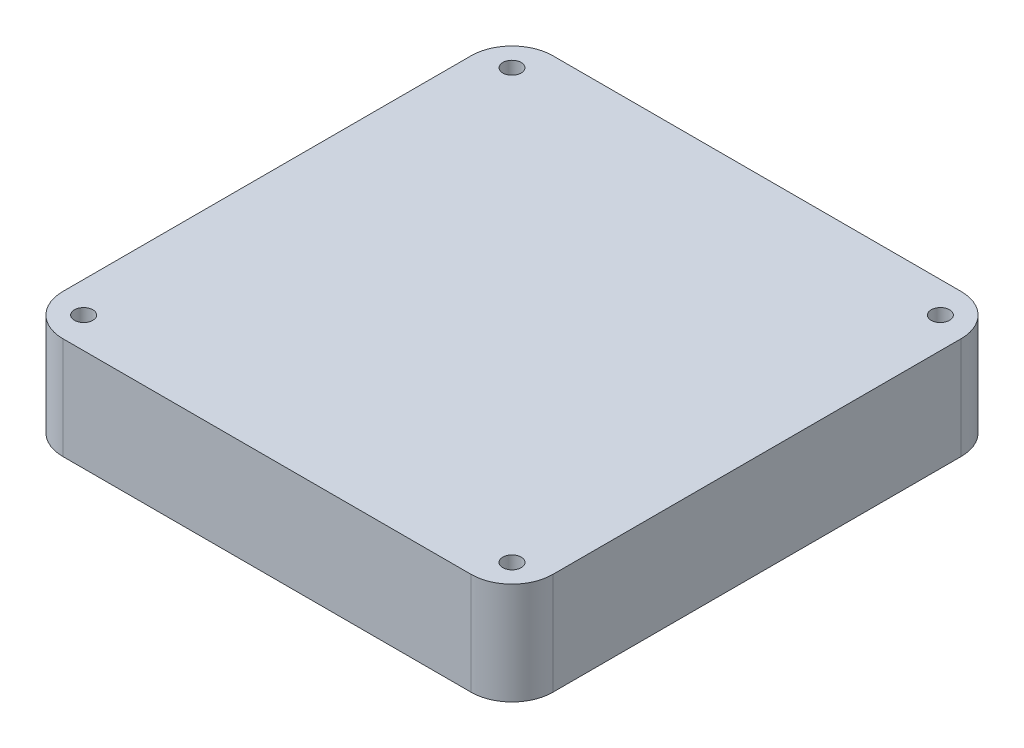
SolidWorks part; units mm, degrees
ref_plane "Спереди" through (0, 0, 0) normal (0, 0, 1) x (1, 0, 0)
ref_plane "Сверху" through (0, 0, 0) normal (0, 1, 0) x (1, 0, 0)
ref_plane "Справа" through (0, 0, 0) normal (1, 0, 0) x (0, 0, -1)
sketch "Эскиз1" plane through (0, 0, 0) normal (0, 1, 0) x (1, 0, 0)
  line L0 (112.45, 60) -> (120, 60) construction
  line L1 (0, 0) -> (120, 0)
  line L2 (0, 0) -> (0, 120)
  line L3 (0, 120) -> (120, 120)
  line L4 (120, 0) -> (120, 120)
  line L5 (7.55, 112.45) -> (112.45, 112.45) construction
  line L6 (7.55, 112.45) -> (7.55, 7.55) construction
  line L7 (7.55, 7.55) -> (112.45, 7.55) construction
  line L8 (112.45, 112.45) -> (112.45, 7.55) construction
  line L9 (60, 112.45) -> (60, 120) construction
  circle A0 centre (7.55, 112.45) radius 2.25
  circle A1 centre (112.45, 112.45) radius 2.25
  circle A2 centre (112.45, 7.55) radius 2.25
  circle A3 centre (7.55, 7.55) radius 2.25
  dimension "D2" = 4.5
  dimension "D1" = 120
  dimension "D3" = 5.3
extrude "Бобышка-Вытянуть1" add sketch "Эскиз1" along normal blind 25
fillet "Скругление1" radius 10 4 edges at (0, 12.5, -120) (120, 12.5, -120) (120, 12.5, 0) (0, 12.5, 0)
